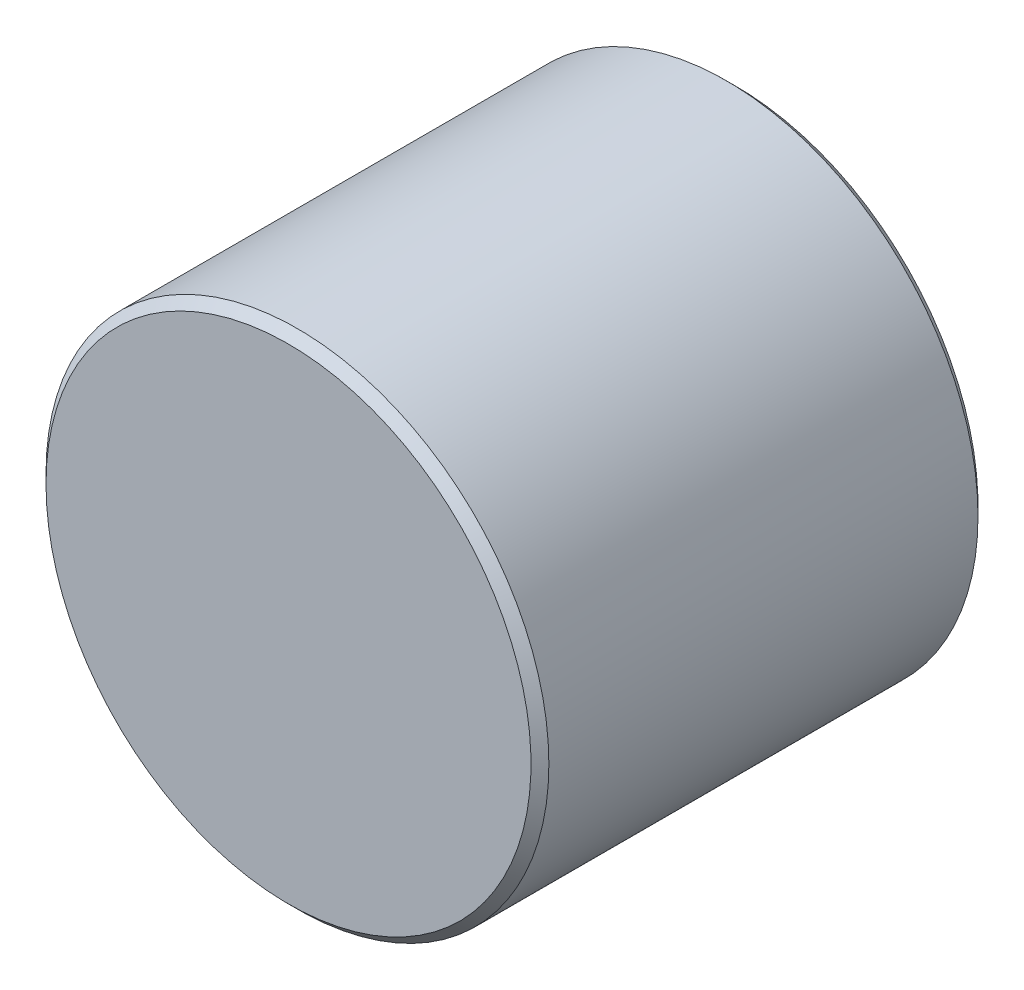
SolidWorks part; units mm, degrees
material "2024 Alloy"
ref_plane "Front Plane" through (0, 0, 0) normal (0, 0, 1) x (1, 0, 0)
ref_plane "Top Plane" through (0, 0, 0) normal (0, 1, 0) x (1, 0, 0)
ref_plane "Right Plane" through (0, 0, 0) normal (1, 0, 0) x (0, 0, -1)
ref_plane "Plane1" through (0, 0, 0) normal (0, -1, 0) x (1, 0, 0)
sketch "Sketch1" plane through (0, 0, 0) normal (0, -1, 0) x (1, 0, 0)
  line L0 (6.8898, 12.7) -> (0, 12.7)
  line L1 (0, 12.7) -> (0, 0)
  line L2 (0, 0) -> (6.8897, 0)
  line L3 (6.8897, 0) -> (7.1437, 0.254)
  line L4 (7.1437, 0.254) -> (7.1437, 12.446)
  line L5 (7.1437, 12.446) -> (6.8898, 12.7)
  line L6 (0, 12.7) -> (0, 0) construction
revolve "Revolve1" add sketch "Sketch1" angle 360 about L6
